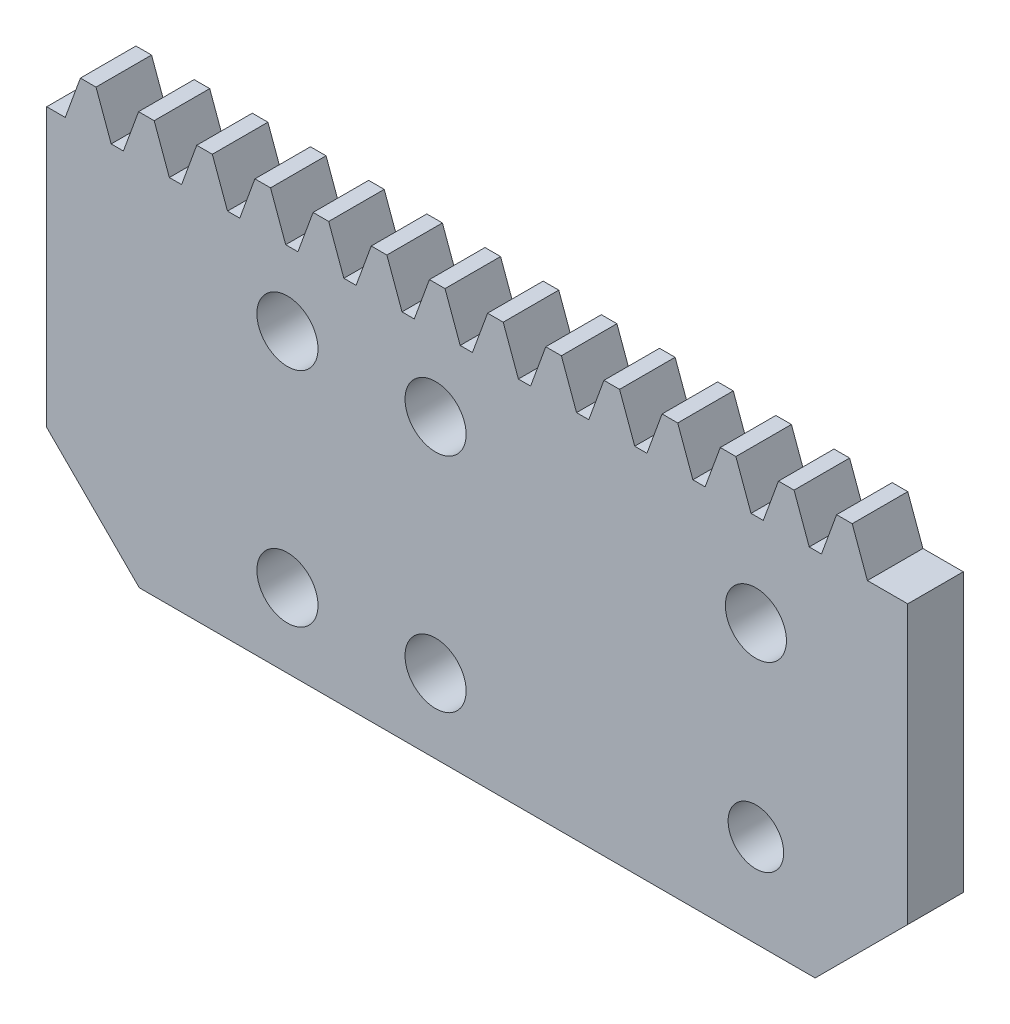
SolidWorks part; units mm, degrees
material "鑄碳鋼"
ref_plane "前基準面" through (0, 0, 0) normal (0, 0, 1) x (1, 0, 0)
ref_plane "上基準面" through (0, 0, 0) normal (0, 1, 0) x (1, 0, 0)
ref_plane "右基準面" through (0, 0, 0) normal (1, 0, 0) x (0, 0, -1)
sketch "草圖1" plane through (0, 0, 0) normal (0, 0, 1) x (1, 0, 0)
  line L1 (-23.25, -10) -> (23.25, -10)
  line L2 (-23.25, -10) -> (-23.25, 10)
  line L3 (-23.25, 10) -> (23.25, 10)
  line L4 (23.25, -10) -> (23.25, 10)
  line L5 (-23.25, -10) -> (23.25, 10) construction
  line L6 (-23.25, 10) -> (23.25, -10) construction
  point P0 (0, 0)
  dimension "D1" = 20
  dimension "D2" = 46.5
extrude "填料-伸長1" add sketch "草圖1" along normal blind 3
sketch "草圖2" plane through (0, 0, 3) normal (0, 0, 1) x (1, 0, 0)
  line L0 (-22.25, 10) -> (-21.4311, 12.25)
  line L1 (23.25, 10) -> (-23.25, 10) construction
  line L2 (-21.4311, 12.25) -> (-20.5882, 12.25)
  line L3 (-20.5882, 12.25) -> (-19.7693, 10)
  line L4 (-22.25, 10) -> (-19.7693, 10)
  line L5 (-21.795, 11.25) -> (-20.2242, 11.25) construction
  dimension "D1" = 1
  dimension "D2" = 1.5708
  dimension "D3" = 2.25
  dimension "D4" = 1
  dimension "D5" = 40
extrude "填料-伸長2" add sketch "草圖2" against normal blind 3
pattern_linear "直線複製排列1" count 14 spacing 3.1416 along (1, 0, 0) of "填料-伸長2"
sketch "草圖3" plane through (0, 0, 3) normal (0, 0, 1) x (1, 0, 0)
  line L0 (-23.25, 10) -> (-23.25, -10) construction
  line L1 (-10.25, 6) -> (-2.25, 6) construction
  line L2 (-10.25, 6) -> (-10.25, -6) construction
  line L3 (-10.25, -6) -> (-2.25, -6) construction
  line L4 (-2.25, 6) -> (-2.25, -6) construction
  circle A0 centre (-10.25, 6) radius 1.65
  circle A1 centre (-2.25, 6) radius 1.65
  circle A2 centre (-2.25, -6) radius 1.65
  circle A3 centre (-10.25, -6) radius 1.65
  point P10 (-10.25, 0)
  point P11 (-23.25, 0)
  dimension "D1" = 3.3
  dimension "D2" = 3.3
  dimension "D3" = 3.3
  dimension "D4" = 3.3
  dimension "D5" = 12
  dimension "D6" = 8
  dimension "D7" = 13
extrude "除料-伸長1" cut sketch "草圖3" against normal blind 3
sketch "草圖4" plane through (0, 0, 3) normal (0, 0, 1) x (1, 0, 0)
  line L0 (15.05, 5) -> (15.05, -5) construction
  line L1 (23.25, -10) -> (23.25, 10) construction
  circle A0 centre (15.05, 5) radius 1.65
  circle A1 centre (15.05, -5) radius 1.5
  point P6 (15.05, 0)
  dimension "D1" = 3.3
  dimension "D2" = 3
  dimension "D3" = 8.2
  dimension "D4" = 10
extrude "除料-伸長2" cut sketch "草圖4" against normal blind 10
chamfer "導角1" distance 5 angle 45 2 edges at (-23.25, -10, 1.5) (23.25, -10, 1.5)
